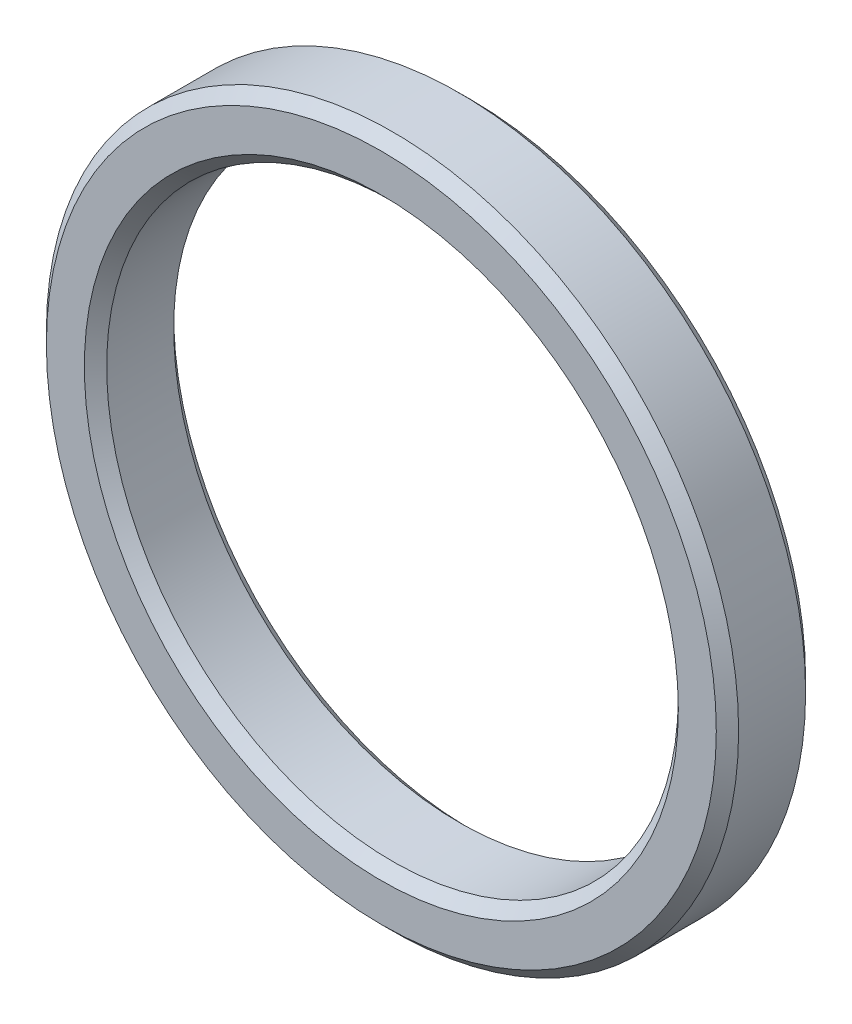
SolidWorks part; units mm, degrees
ref_plane "Front Plane" through (0, 0, 0) normal (0, 0, 1) x (1, 0, 0)
ref_plane "Top Plane" through (0, 0, 0) normal (0, 1, 0) x (1, 0, 0)
ref_plane "Right Plane" through (0, 0, 0) normal (1, 0, 0) x (0, 0, -1)
sketch "Sketch1" plane through (0, 0, 0) normal (0, 0, 1) x (1, 0, 0)
  circle A0 centre (0, 0) radius 12.8
  circle A1 centre (0, 0) radius 15.5
  dimension "D1" = 25.6
  dimension "D2" = 31
extrude "Boss-Extrude1" add sketch "Sketch1" along normal blind 4
chamfer "Chamfer1" distance 0.5 angle 45 4 edges at (12.8, 0, 0) (15.5, 0, 0) (12.8, 0, 4) (15.5, 0, 4)
